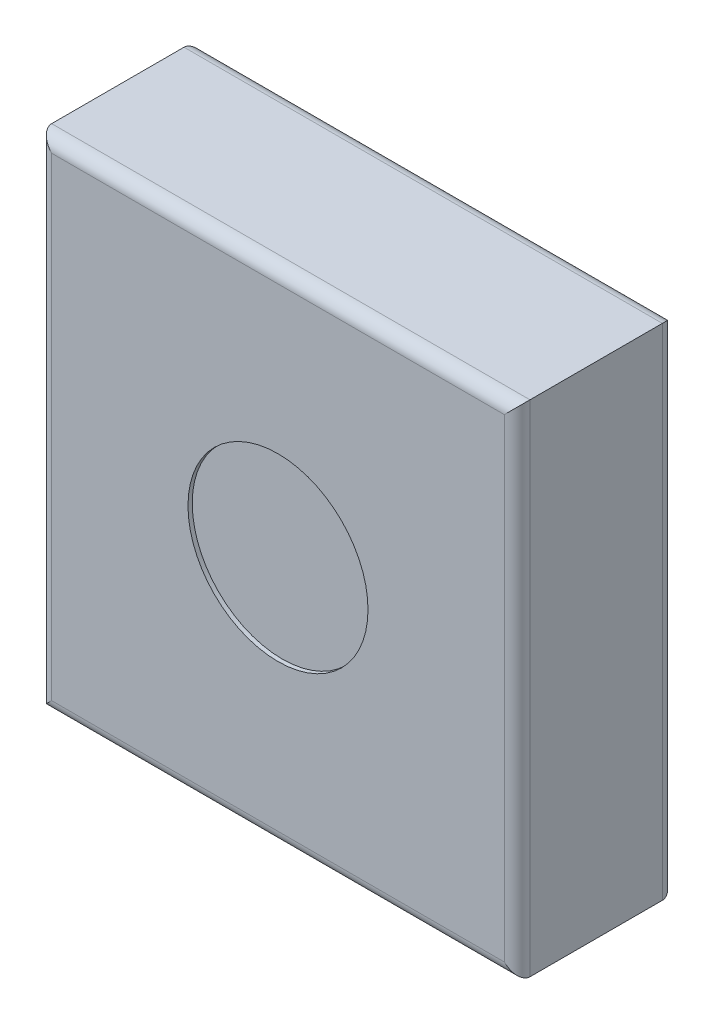
SolidWorks part; units mm, degrees
ref_plane "前视基准面" through (0, 0, 0) normal (0, 0, 1) x (1, 0, 0)
ref_plane "上视基准面" through (0, 0, 0) normal (0, 1, 0) x (1, 0, 0)
ref_plane "右视基准面" through (0, 0, 0) normal (1, 0, 0) x (0, 0, -1)
sketch "草图1" plane through (0, 0, 0) normal (0, 0, 1) x (1, 0, 0)
  line L1 (-56, 58.5) -> (56, 58.5)
  line L2 (-56, 58.5) -> (-56, -58.5)
  line L3 (-56, -58.5) -> (56, -58.5)
  line L4 (56, 58.5) -> (56, -58.5)
  line L5 (-56, 58.5) -> (56, -58.5) construction
  line L6 (-56, -58.5) -> (56, 58.5) construction
  point P0 (0, 0)
  dimension "D1" = 112
  dimension "D2" = 117
extrude "凸台-拉伸1" add sketch "草图1" along normal blind 37
fillet "圆角1" radius 3 4 edges at (0, -58.5, 37) (-56, 0, 37) (0, 58.5, 37) (56, 0, 37)
fillet "圆角2" radius 3 4 edges at (0, 58.5, 0) (-56, 0, 0) (0, -58.5, 0) (56, 0, 0)
sketch "草图2" plane through (0, 0, 37) normal (0, 0, 1) x (1, 0, 0)
  circle A0 centre (0, 0) radius 21.0746
extrude "切除-拉伸1" cut sketch "草图2" against normal blind 1
